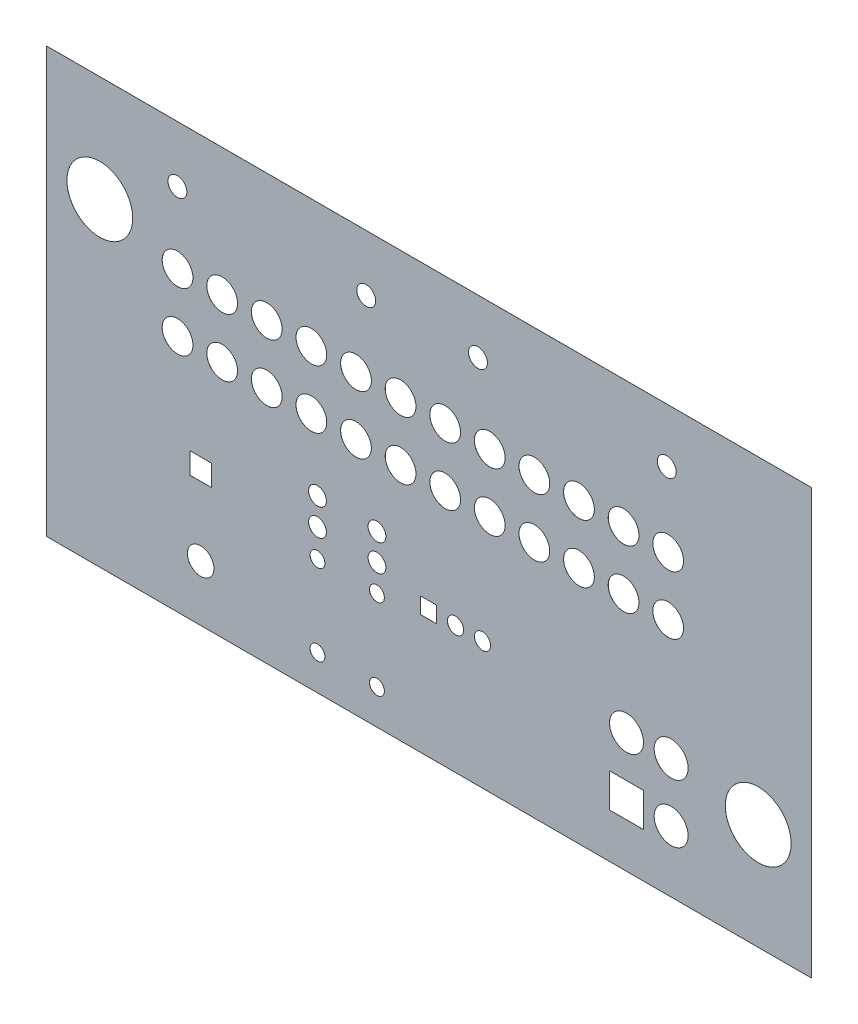
SolidWorks part; units mm, degrees
ref_plane "Front Plane" through (0, 0, 0) normal (0, 0, 1) x (1, 0, 0)
ref_plane "Top Plane" through (0, 0, 0) normal (0, 1, 0) x (1, 0, 0)
ref_plane "Right Plane" through (0, 0, 0) normal (1, 0, 0) x (0, 0, -1)
sketch "Sketch1" plane through (0, 0, 0) normal (0, 0, 1) x (1, 0, 0)
  line L0 (60625, 33355) -> (61885, 32095) construction
  line L1 (61885, 33355) -> (60625, 32095) construction
  line L2 (45075, 35854) -> (45861, 35068) construction
  line L3 (45861, 35854) -> (45075, 35068) construction
  line L4 (53617, 35466) -> (54217, 34866) construction
  line L5 (54217, 35466) -> (53617, 34866) construction
  line L8 (53617, 35466) -> (53617, 34866)
  line L9 (53617, 34866) -> (54217, 34866)
  line L10 (54217, 34866) -> (54217, 35466)
  line L11 (54217, 35466) -> (53617, 35466)
  line L12 (45861, 35854) -> (45075, 35854)
  line L13 (45075, 35854) -> (45075, 35068)
  line L14 (45075, 35068) -> (45861, 35068)
  line L15 (45861, 35068) -> (45861, 35854)
  line L16 (60625, 33355) -> (60625, 32095)
  line L17 (60625, 32095) -> (61885, 32095)
  line L18 (61885, 32095) -> (61885, 33355)
  line L19 (61885, 33355) -> (60625, 33355)
  line L1295 (39759, 46190) -> (68105, 46190)
  line L1296 (39759, 46190) -> (39759, 30442)
  line L1297 (39759, 30442) -> (68105, 30442)
  line L1298 (68105, 46190) -> (68105, 30442)
  circle A0 centre (54917, 35166) radius 300
  circle A1 centre (55917, 35166) radius 300
  circle A2 centre (62799, 39296) radius 570
  circle A3 centre (61146, 39296) radius 570
  circle A4 centre (59492, 39296) radius 570
  circle A5 centre (57839, 39296) radius 570
  circle A6 centre (56185, 39296) radius 570
  circle A7 centre (54532, 39296) radius 570
  circle A8 centre (52879, 39296) radius 570
  circle A9 centre (51226, 39296) radius 570
  circle A10 centre (49572, 39296) radius 570
  circle A11 centre (47919, 39296) radius 570
  circle A12 centre (46265, 39296) radius 570
  circle A13 centre (44611, 39296) radius 570
  circle A14 centre (62799, 41461) radius 570
  circle A15 centre (61146, 41461) radius 570
  circle A16 centre (59492, 41461) radius 570
  circle A17 centre (57839, 41461) radius 570
  circle A18 centre (56185, 41461) radius 570
  circle A19 centre (54532, 41461) radius 570
  circle A20 centre (52879, 41461) radius 570
  circle A21 centre (51226, 41461) radius 570
  circle A22 centre (49572, 41461) radius 570
  circle A23 centre (47919, 41461) radius 570
  circle A24 centre (46265, 41461) radius 570
  circle A25 centre (44611, 41461) radius 570
  circle A26 centre (44605, 44103) radius 350
  circle A27 centre (51605, 44103) radius 350
  circle A28 centre (62747, 44182) radius 350
  circle A29 centre (55747, 44182) radius 350
  circle A30 centre (52003, 34737) radius 275
  circle A31 centre (52003, 31737) radius 275
  circle A32 centre (49798, 34737) radius 275
  circle A33 centre (49798, 31737) radius 275
  circle A34 centre (52003, 36729) radius 330
  circle A35 centre (52003, 35729) radius 330
  circle A36 centre (49798, 36768) radius 330
  circle A37 centre (49798, 35768) radius 330
  circle A38 centre (45468, 32509) radius 492
  circle A39 centre (41728, 42253) radius 1220
  circle A40 centre (66137, 34379) radius 1220
  circle A41 centre (62909, 32725) radius 630
  circle A42 centre (61255, 34890) radius 630
  circle A43 centre (62909, 34890) radius 630
extrude "Boss-Extrude1" add sketch "Sketch1" along normal blind 1.6
